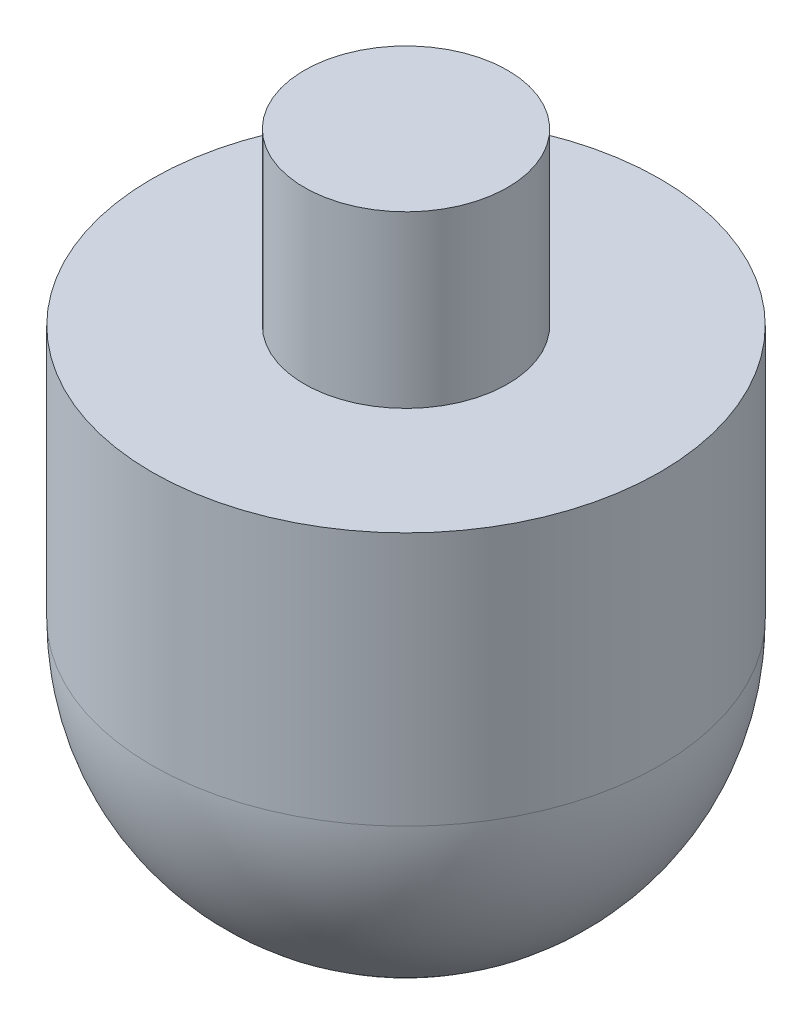
SolidWorks part; units mm, degrees
ref_plane "Front Plane" through (0, 0, 0) normal (0, 0, 1) x (1, 0, 0)
ref_plane "Top Plane" through (0, 0, 0) normal (0, 1, 0) x (1, 0, 0)
ref_plane "Right Plane" through (0, 0, 0) normal (1, 0, 0) x (0, 0, -1)
sketch "Sketch1" plane through (0, 0, 0) normal (0, 0, 1) x (1, 0, 0)
  line L0 (0, 0) -> (0, 436.3009) construction
  line L2 (150, 0) -> (150, 150)
  line L3 (150, 150) -> (60, 150)
  line L4 (60, 150) -> (60, 250.5296)
  line L5 (60, 250.5296) -> (0, 250.5296)
  line L6 (0, 250.5296) -> (0, -150)
  arc A0 (0, -150) -> (150, 0) centre (0, 0) ccw
  dimension "D2" = 120
  dimension "D1" = 150
revolve "Revolve1" add sketch "Sketch1" angle 360 about L0
